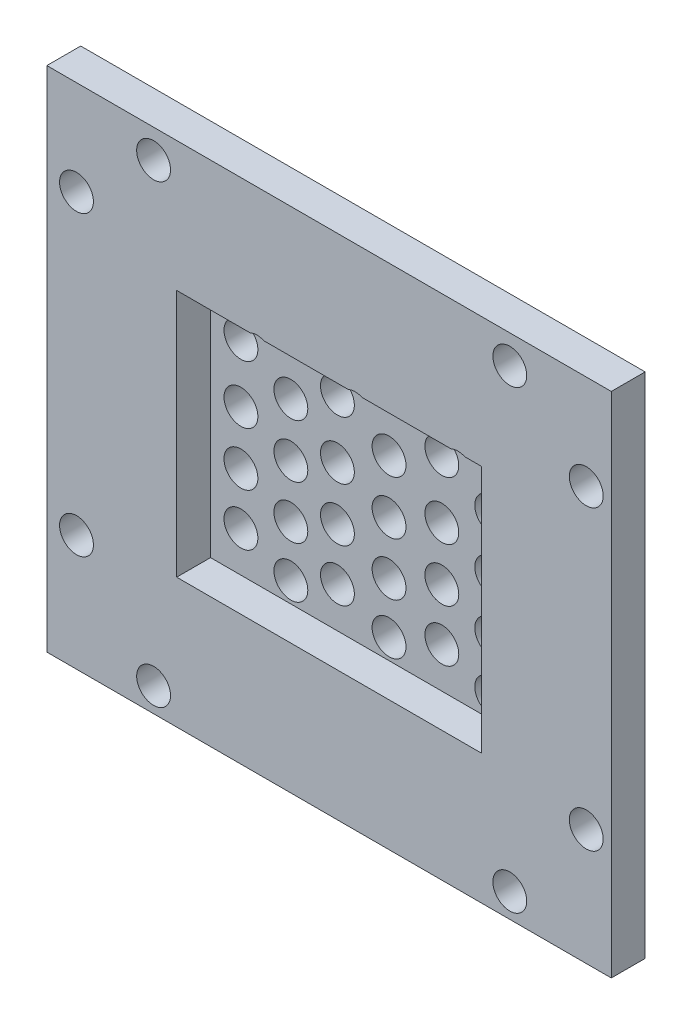
SolidWorks part; units mm, degrees
other "Markup1"
sketch "Sketch20" plane through (22.5, 20, 0) normal (0.0342, 0.0154, -0.9993) x (0.6764, -0.7364, 0.0118)
ref_plane "Front Plane" through (0, 0, 0) normal (0, 0, 1) x (1, 0, 0)
ref_plane "Top Plane" through (0, 0, 0) normal (0, 1, 0) x (1, 0, 0)
ref_plane "Right Plane" through (0, 0, 0) normal (1, 0, 0) x (0, 0, -1)
sketch "Sketch1" plane through (0, 0, 0) normal (0, 0, 1) x (1, 0, 0)
  line L1 (-25, 22.5) -> (25, 22.5)
  line L2 (-25, 22.5) -> (-25, -22.5)
  line L3 (-25, -22.5) -> (25, -22.5)
  line L4 (25, 22.5) -> (25, -22.5)
  line L5 (-25, 22.5) -> (25, -22.5) construction
  line L6 (-25, -22.5) -> (25, 22.5) construction
  point P0 (0, 0)
  dimension "D1" = 50
  dimension "D2" = 45
extrude "Boss-Extrude1" add sketch "Sketch1" along normal blind 6
sketch "Sketch2" plane through (0, 0, 0) normal (0, 0, -1) x (-1, 0, 0)
  line L1 (20, -17.5) -> (-20, -17.5)
  line L2 (20, -17.5) -> (20, 17.5)
  line L3 (20, 17.5) -> (-20, 17.5)
  line L4 (-20, -17.5) -> (-20, 17.5)
  line L5 (20, -17.5) -> (-20, 17.5) construction
  line L6 (20, 17.5) -> (-20, -17.5) construction
  line L7 (15, -13.125) -> (-15, -13.125)
  line L8 (15, -13.125) -> (15, 13.125)
  line L9 (15, 13.125) -> (-15, 13.125)
  line L10 (-15, -13.125) -> (-15, 13.125)
  line L11 (15, -13.125) -> (-15, 13.125) construction
  line L12 (15, 13.125) -> (-15, -13.125) construction
  point P0 (0, 0)
  point P6 (0, 0)
  dimension "D1" = 40
  dimension "D2" = 35
  dimension "D3" = 30
extrude "Cut-Extrude1" cut sketch "Sketch2" against normal blind 5
sketch "Sketch8" plane through (0, 0, 6) normal (0, 0, 1) x (1, 0, 0)
  line L1 (-13.5, 11) -> (13.5, 11)
  line L2 (-13.5, 11) -> (-13.5, -11)
  line L3 (-13.5, -11) -> (13.5, -11)
  line L4 (13.5, 11) -> (13.5, -11)
  line L5 (-13.5, 11) -> (13.5, -11) construction
  line L6 (-13.5, -11) -> (13.5, 11) construction
  point P0 (0, 0)
  dimension "D1" = 27
  dimension "D2" = 22
extrude "Cut-Extrude2" cut sketch "Sketch8" against normal blind 3
sketch "Sketch19" plane through (0, 0, 0) normal (0, 0, -1) x (-1, 0, 0)
  line L1 (25, 22.5) -> (-25, 22.5)
  line L2 (25, 22.5) -> (25, -22.5)
  line L3 (25, -22.5) -> (-25, -22.5)
  line L4 (-25, 22.5) -> (-25, -22.5)
  line L5 (20, 17.5) -> (-20, 17.5)
  line L6 (20, 17.5) -> (20, -17.5)
  line L7 (20, -17.5) -> (-20, -17.5)
  line L8 (-20, 17.5) -> (-20, -17.5)
extrude "Cut-Extrude3" cut sketch "Sketch19" against normal blind 3
hole_wizard "Ø3.0mm Dowel Hole1" positions "Sketch21" profile "Sketch22" hole size "Ø3.0" standard "ANSI Metric" end condition through all
sketch "Sketch21" plane through (0, 0, 3) normal (0, 0, -1) x (-1, 0, 0)
  point P0 (-22.7831, 14.1236)
  point P2 (-22.7831, -12.2112)
  point P4 (-16.011, -20.3583)
  point P6 (15.5445, -20.3583)
  point P8 (22.3743, -12.2112)
  point P10 (22.3743, 14.1236)
  point P12 (15.5445, 19.9715)
  point P14 (-16.011, 19.9715)
sketch "Sketch22" plane through (22.7831, 14.1236, 3) normal (1, 0, 0) x (0, 1, 0)
  line L0 (0, 0) -> (0, 3)
  line L1 (0, 3) -> (1.5, 3)
  line L2 (1.5, 3) -> (1.5, 0)
  line L5 (1.5, 0) -> (0, 0)
  line L11 (0, -6.35) -> (0, 107.95) construction
  dimension "Thru Hole Dia." = 3
  dimension "Thru Hole Depth" = 3
hole_wizard "Ø3.0mm Dowel Hole2" positions "Sketch23" profile "Sketch24" hole size "Ø3.0" standard "ANSI Metric" end condition through all
sketch "Sketch23" plane through (0, 0, 0) normal (0, 0, -1) x (-1, 0, 0)
  point P0 (-11.4094, 9.6321)
  point P2 (-11.4094, 4.7335)
  point P4 (-11.4094, 0)
  point P6 (-11.4094, -4.6889)
  point P8 (-11.4094, -9.1984)
  point P10 (-6.9886, 7.0563)
  point P12 (-6.9886, 1.9165)
  point P14 (-6.9886, -2.82)
  point P16 (-6.9886, -7.4187)
  point P18 (-2.3143, 9.6321)
  point P20 (-2.3143, 4.7335)
  point P22 (2.2604, 7.0563)
  point P24 (6.3855, 9.6321)
  point P26 (6.3855, 4.7335)
  point P28 (10.8084, 7.0563)
  point P30 (-2.3143, 0)
  point P32 (-2.3143, -4.6889)
  point P34 (-2.3143, -9.1984)
  point P36 (2.2604, 1.9165)
  point P38 (2.2604, -2.82)
  point P40 (2.2604, -7.4187)
  point P42 (6.3855, 0)
  point P44 (6.3855, -4.6889)
  point P46 (6.3855, -9.1984)
  point P48 (10.8084, 1.9165)
  point P50 (10.8084, -2.82)
  point P52 (10.8084, -7.4187)
sketch "Sketch24" plane through (11.4094, 9.6321, 0) normal (1, 0, 0) x (0, 1, 0)
  line L0 (0, 0) -> (0, 6)
  line L1 (0, 6) -> (1.5, 6)
  line L2 (1.5, 6) -> (1.5, 0)
  line L5 (1.5, 0) -> (0, 0)
  line L11 (0, -6.35) -> (0, 107.95) construction
  dimension "Thru Hole Dia." = 3
  dimension "Thru Hole Depth" = 6
